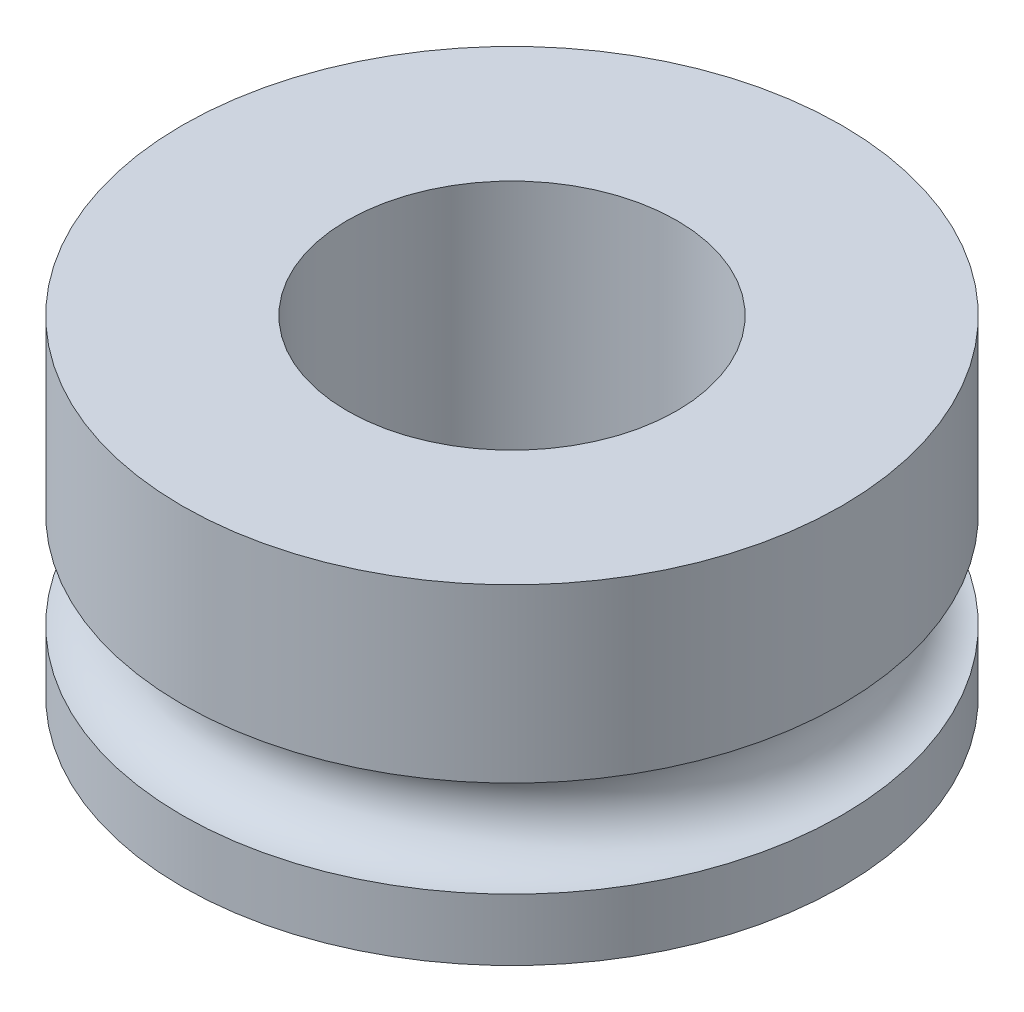
SolidWorks part; units mm, degrees
ref_plane "Front Plane" through (0, 0, 0) normal (0, 0, 1) x (1, 0, 0)
ref_plane "Top Plane" through (0, 0, 0) normal (0, 1, 0) x (1, 0, 0)
ref_plane "Right Plane" through (0, 0, 0) normal (1, 0, 0) x (0, 0, -1)
sketch "Sketch1" plane through (0, 0, 0) normal (0, 1, 0) x (1, 0, 0)
  circle A0 centre (0, 0) radius 6
  dimension "D1" = 12
extrude "Boss-Extrude1" add sketch "Sketch1" along normal blind 6
sketch "Sketch2" plane through (0, 0, 0) normal (0, 0, 1) x (1, 0, 0)
  line L0 (0, 0) -> (0, 6) construction
  line L1 (-6, 0) -> (6, 0) construction
  line L2 (6, 6) -> (-6, 6) construction
  line L3 (0, 2) -> (6, 2) construction
  line L4 (6, 0) -> (6, 6) construction
  circle A0 centre (6, 2) radius 0.875
  dimension "D2" = 1.75
  dimension "D1" = 2
revolve "Cut-Revolve1" cut sketch "Sketch2" angle 360 about L0
sketch "Sketch4" plane through (0, 6, 0) normal (0, 1, 0) x (1, 0, 0)
  line L0 (0.6312, 2.3155) -> (-0.789, -2.8944) construction
  line L2 (-2.8944, 0.789) -> (2.8944, -0.789) construction
  circle A0 centre (0, 0) radius 3
  point P6 (0, 0)
  dimension "D1" = 6
extrude "Cut-Extrude1" cut sketch "Sketch4" against normal blind 8
